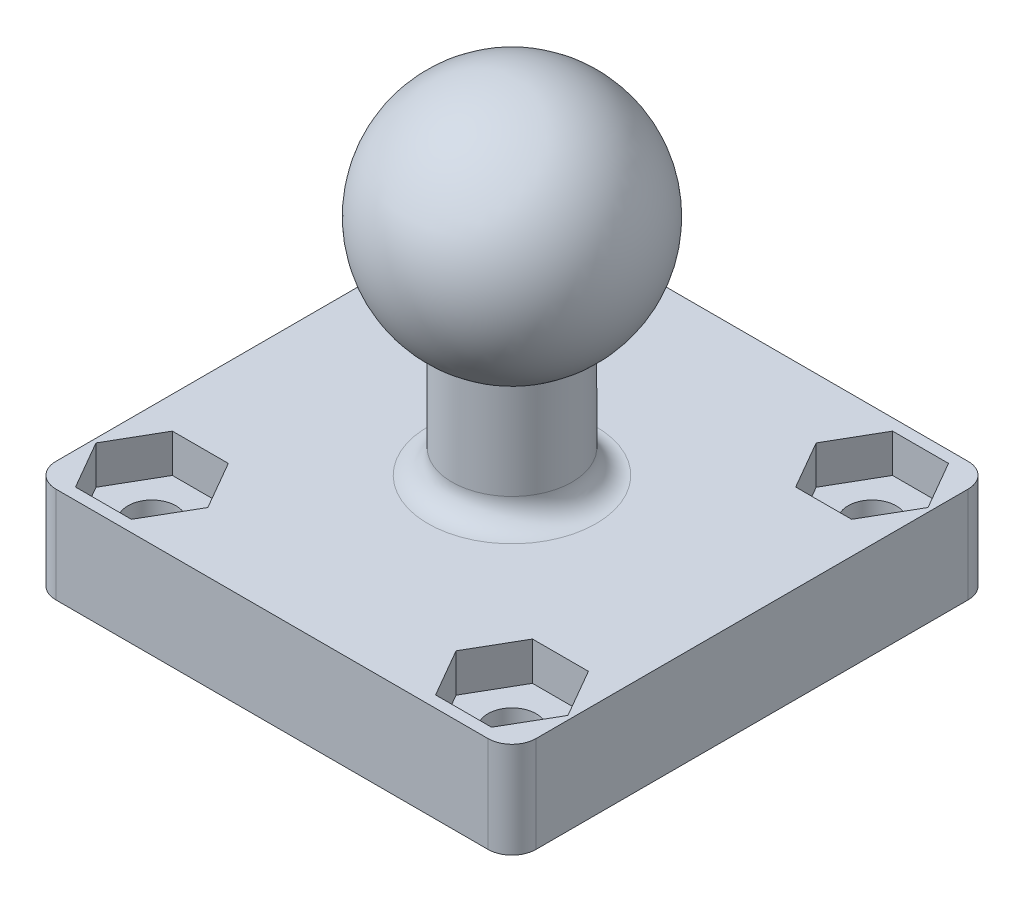
SolidWorks part; units mm, degrees
ref_plane "Plan de face" through (0, 0, 0) normal (0, 0, 1) x (1, 0, 0)
ref_plane "Plan de dessus" through (0, 0, 0) normal (0, 1, 0) x (1, 0, 0)
ref_plane "Plan de droite" through (0, 0, 0) normal (1, 0, 0) x (0, 0, -1)
sketch "Esquisse1" plane through (0, 0, 0) normal (0, 0, 1) x (1, 0, 0)
  line L0 (-2.5, -4.3301) -> (-2.5, -9.3301)
  line L1 (-2.5, -9.3301) -> (0, -9.3301)
  line L2 (0, -9.3301) -> (0, 5)
  line L3 (0, 5) -> (-7.2649, 5) construction
  arc A0 (0, 5) -> (-2.5, -4.3301) centre (0, 0) ccw
  dimension "D1" = 5
  dimension "D2" = 5
  dimension "D3" = 2.5
revolve "Révolution1" add sketch "Esquisse1" angle 360 about L2
sketch "Esquisse2" plane through (0, -9.3301, 0) normal (0, -1, 0) x (1, 0, 0)
  line L1 (-10, 10) -> (10, 10)
  line L2 (-10, 10) -> (-10, -10)
  line L3 (-10, -10) -> (10, -10)
  line L4 (10, 10) -> (10, -10)
  circle A0 centre (0, 0) radius 2.5 construction
  dimension "D3" = 10
  dimension "D4" = 10
  dimension "D1" = 20
  dimension "D2" = 20
extrude "Boss.-Extru.1" add sketch "Esquisse2" along normal blind 4
sketch "Esquisse3" plane through (0, -9.3301, 0) normal (0, 1, 0) x (1, 0, 0)
  circle A0 centre (7.5, -7.5) radius 1
  circle A1 centre (7.5, 7.5) radius 1
  circle A2 centre (-7.5, 7.5) radius 1
  circle A3 centre (-7.5, -7.5) radius 1
  circle A4 centre (0, 0) radius 2.5 construction
  dimension "D1" = 2
  dimension "D2" = 15
  dimension "D3" = 15
  dimension "D4" = 7.5
  dimension "D5" = 7.5
extrude "Enlèv. mat.-Extru.1" cut sketch "Esquisse3" against normal up to next
fillet "Congé1" radius 1 5 edges at (-10, -11.3301, -10) (2.5, -9.3301, 0) (10, -11.3301, -10) (10, -11.3301, 10) (-10, -11.3301, 10)
sketch "Esquisse4" plane through (0, -9.3301, 0) normal (0, 1, 0) x (1, 0, 0)
  line L0 (-9, 10) -> (9, 10) construction
  line L1 (-6.335, -5.4822) -> (-8.665, -5.4822)
  line L2 (-8.665, -5.4822) -> (-9.83, -7.5)
  line L3 (-9.83, -7.5) -> (-8.665, -9.5178)
  line L4 (-8.665, -9.5178) -> (-6.335, -9.5178)
  line L5 (-6.335, -9.5178) -> (-5.17, -7.5)
  line L6 (-5.17, -7.5) -> (-6.335, -5.4822)
  line L7 (9.83, -7.5) -> (8.665, -5.4822)
  line L8 (8.665, -5.4822) -> (6.335, -5.4822)
  line L9 (6.335, -5.4822) -> (5.17, -7.5)
  line L10 (5.17, -7.5) -> (6.335, -9.5178)
  line L11 (6.335, -9.5178) -> (8.665, -9.5178)
  line L12 (8.665, -9.5178) -> (9.83, -7.5)
  line L13 (8.665, 5.4822) -> (9.83, 7.5)
  line L14 (9.83, 7.5) -> (8.665, 9.5178)
  line L15 (8.665, 9.5178) -> (6.335, 9.5178)
  line L16 (6.335, 9.5178) -> (5.17, 7.5)
  line L17 (5.17, 7.5) -> (6.335, 5.4822)
  line L18 (6.335, 5.4822) -> (8.665, 5.4822)
  line L19 (-5.17, 7.5) -> (-6.335, 9.5178)
  line L20 (-6.335, 9.5178) -> (-8.665, 9.5178)
  line L21 (-8.665, 9.5178) -> (-9.83, 7.5)
  line L22 (-9.83, 7.5) -> (-8.665, 5.4822)
  line L23 (-8.665, 5.4822) -> (-6.335, 5.4822)
  line L24 (-6.335, 5.4822) -> (-5.17, 7.5)
  line L27 (9, -10) -> (-9, -10) construction
  circle A0 centre (-7.5, -7.5) radius 2.0178 construction
  circle A1 centre (7.5, -7.5) radius 2.0178 construction
  circle A2 centre (7.5, 7.5) radius 2.0178 construction
  circle A3 centre (-7.5, 7.5) radius 2.0178 construction
  point P39 (0, 0)
  point P42 (0, 0)
  point P43 (0, 0)
  point P44 (0, 0)
  point P45 (0, 0)
  point P51 (0, 0)
  dimension "D1" = 2.33
  dimension "D2" = 2.33
  dimension "D3" = 2.33
  dimension "D4" = 2.33
extrude "Enlèv. mat.-Extru.2" cut sketch "Esquisse4" against normal blind 1.6
